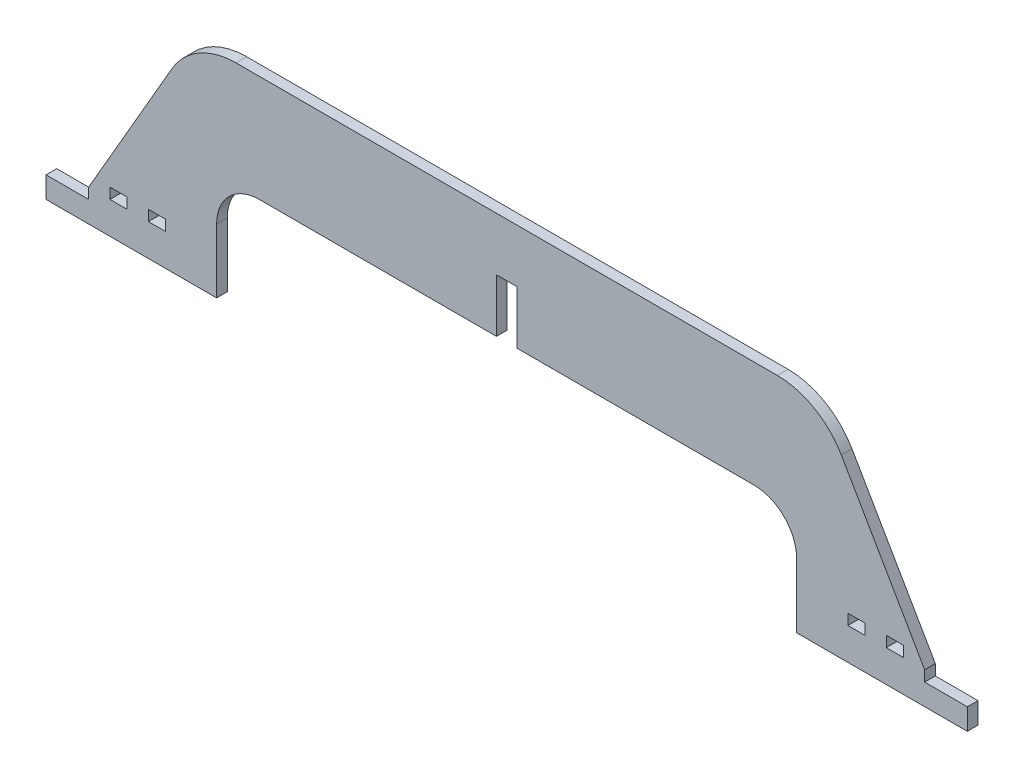
SolidWorks part; units mm, degrees
ref_plane "前视基准面" through (0, 0, 0) normal (0, 0, 1) x (1, 0, 0)
ref_plane "上视基准面" through (0, 0, 0) normal (0, 1, 0) x (1, 0, 0)
ref_plane "右视基准面" through (0, 0, 0) normal (1, 0, 0) x (0, 0, -1)
sketch "草图1" plane through (0, 0, 0) normal (0, 0, 1) x (1, 0, 0)
  line L12 (0, 256.6802) -> (0, -57.0056) construction
  line L13 (-216, 0) -> (-216, 10)
  line L14 (-216, 10) -> (-196, 10)
  line L15 (-196, 10) -> (-196, 15)
  line L17 (-196, 15) -> (-146.9252, 100)
  line L18 (-146.9252, 100) -> (146.9252, 100)
  line L20 (136, 50) -> (-136, 50)
  line L21 (-136, 50) -> (-136, 0)
  line L22 (-136, 0) -> (-216, 0)
  line L23 (136, 50) -> (136, 0)
  line L24 (136, 0) -> (216, 0)
  line L25 (216, 0) -> (216, 10)
  line L26 (216, 10) -> (196, 10)
  line L27 (196, 10) -> (196, 15)
  line L29 (196, 15) -> (146.9252, 100)
  dimension "D1" = 10
  dimension "D2" = 5
  dimension "D3" = 20
  dimension "D4" = 50
  dimension "D5" = 392
  dimension "D6" = 80
  dimension "D7" = 100
  dimension "D8" = 60
extrude "凸台-拉伸1" add sketch "草图1" along normal blind 5
sketch "草图2" plane through (0, 0, 5) normal (0, 0, 1) x (1, 0, 0)
  line L0 (-146.9252, 100) -> (-126.9252, 100)
  line L1 (146.9252, 100) -> (-146.9252, 100) construction
  line L2 (-146.9252, 100) -> (-156.9252, 82.6795)
  line L3 (-146.9252, 100) -> (-196, 15) construction
  line L4 (0, 114.8473) -> (0, -48.9602) construction
  line L5 (146.9252, 100) -> (156.9252, 82.6795)
  line L6 (146.9252, 100) -> (126.9252, 100)
  arc A0 (-126.9252, 100) -> (-156.9252, 82.6795) centre (-126.9252, 65.359) ccw
  arc A1 (126.9252, 100) -> (156.9252, 82.6795) centre (126.9252, 65.359) cw
  dimension "D1" = 20
extrude "切除-拉伸1" cut sketch "草图2" against normal up to next
sketch "草图3" plane through (0, 0, 5) normal (0, 0, 1) x (1, 0, 0)
  line L0 (-116, 50) -> (-136, 50)
  line L1 (-136, 50) -> (136, 50) construction
  line L2 (-136, 50) -> (-136, 30)
  line L3 (-136, 0) -> (-136, 50) construction
  line L4 (0, 39.1826) -> (0, -70.8264) construction
  line L5 (136, 50) -> (136, 30)
  line L6 (116, 50) -> (136, 50)
  arc A0 (-116, 50) -> (-136, 30) centre (-116, 30) ccw
  arc A1 (116, 50) -> (136, 30) centre (116, 30) cw
  dimension "D1" = 20
extrude "凸台-拉伸2" add sketch "草图3" against normal up to surface (5 mm away) up to face at (0, 33.9623, 0)
sketch "草图4" plane through (0, 0, 5) normal (0, 0, 1) x (1, 0, 0)
  line L1 (-4.8, 25) -> (4.8, 25)
  line L2 (-4.8, 25) -> (-4.8, 75)
  line L3 (-4.8, 75) -> (4.8, 75)
  line L4 (4.8, 25) -> (4.8, 75)
  line L5 (-4.8, 25) -> (4.8, 75) construction
  line L6 (-4.8, 75) -> (4.8, 25) construction
  line L7 (-116, 50) -> (116, 50) construction
  point P0 (0, 50)
  point P5 (0, 0)
  point P7 (0, 0)
  point P9 (-26.1636, 50)
  point P10 (0, 0)
  dimension "D1" = 9.6
  dimension "D2" = 25
extrude "切除-拉伸2" cut sketch "草图4" against normal up to next
sketch "草图5" plane through (0, 0, 5) normal (0, 0, 1) x (1, 0, 0)
  line L1 (-186, 15) -> (-178, 15)
  line L2 (-186, 15) -> (-186, 20)
  line L3 (-186, 20) -> (-178, 20)
  line L4 (-178, 15) -> (-178, 20)
  line L5 (-186, 15) -> (-178, 20) construction
  line L6 (-186, 20) -> (-178, 15) construction
  line L7 (-168, 15) -> (-160, 15)
  line L8 (-168, 15) -> (-168, 20)
  line L9 (-168, 20) -> (-160, 20)
  line L10 (-160, 15) -> (-160, 20)
  line L11 (-168, 15) -> (-160, 20) construction
  line L12 (-168, 20) -> (-160, 15) construction
  line L13 (-196, 15) -> (-196, 10) construction
  line L14 (0, 34.0417) -> (0, -50.9257) construction
  line L15 (168, 20) -> (160, 20)
  line L16 (160, 15) -> (160, 20)
  line L17 (168, 15) -> (160, 15)
  line L18 (168, 15) -> (168, 20)
  line L19 (186, 20) -> (178, 20)
  line L20 (178, 15) -> (178, 20)
  line L21 (186, 15) -> (178, 15)
  line L22 (186, 15) -> (186, 20)
  line L23 (-196, 10) -> (-216, 10) construction
  point P4 (-182, 17.5)
  point P9 (-164, 17.5)
  dimension "D1" = 8
  dimension "D2" = 8
  dimension "D3" = 5
  dimension "D4" = 5
  dimension "D5" = 10
  dimension "D6" = 10
  dimension "D7" = 5
extrude "切除-拉伸3" cut sketch "草图5" against normal up to next
